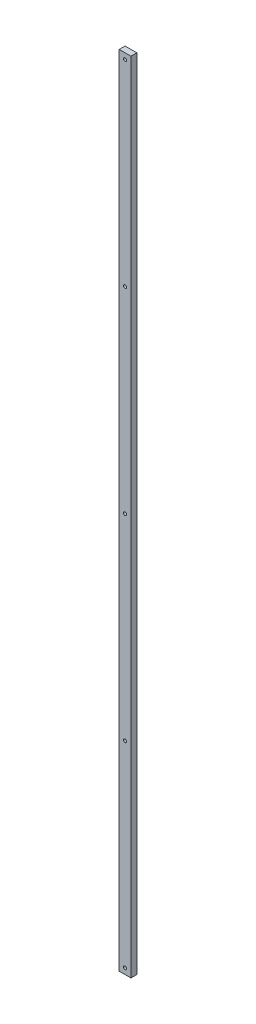
SolidWorks part; units mm, degrees
material "PE High Density"
ref_plane "Front Plane" through (0, 0, 0) normal (0, 0, 1) x (1, 0, 0)
ref_plane "Top Plane" through (0, 0, 0) normal (0, 1, 0) x (1, 0, 0)
ref_plane "Right Plane" through (0, 0, 0) normal (1, 0, 0) x (0, 0, -1)
sketch "Sketch1" plane through (0, 0, 0) normal (0, 0, 1) x (1, 0, 0)
  line L0 (0, 0) -> (25.4, 0)
  line L1 (25.4, 0) -> (25.4, 1727.2)
  line L5 (0, 1727.2) -> (0, 0)
  line L6 (0, 1727.2) -> (25.4, 1727.2)
  dimension "D2" = 25.4
  dimension "D4" = 1727.2
extrude "Boss-Extrude1" add sketch "Sketch1" along normal blind 12.7
sketch "Sketch2" plane through (0, 0, 12.7) normal (0, 0, 1) x (1, 0, 0)
  line L0 (25.4, 0) -> (25.4, 1727.2) construction
  line L1 (0, 0) -> (25.4, 0) construction
  circle A0 centre (12.7, 12.7) radius 3.3655
  dimension "D1" = 6.731
  dimension "D2" = 12.7
  dimension "D3" = 12.7
extrude "Cut-Extrude1" cut sketch "Sketch2" against normal through all
pattern_linear "LPattern1" count 5 spacing 425.45 along (0, 1, 0) of "Cut-Extrude1"
